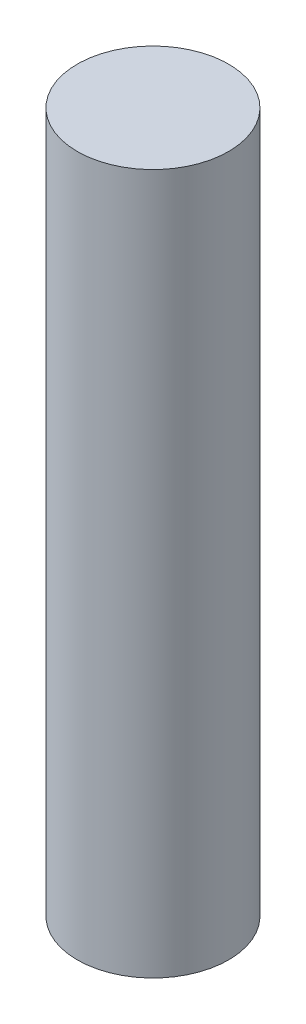
SolidWorks part; units mm, degrees
ref_plane "Front Plane" through (0, 0, 0) normal (0, 0, 1) x (1, 0, 0)
ref_plane "Top Plane" through (0, 0, 0) normal (0, 1, 0) x (1, 0, 0)
ref_plane "Right Plane" through (0, 0, 0) normal (1, 0, 0) x (0, 0, -1)
sketch "Sketch1" plane through (0, 0, 0) normal (0, 1, 0) x (1, 0, 0)
  circle A0 centre (0, 0) radius 0.4
  dimension "D1" = 0.8
extrude "Boss-Extrude1" add sketch "Sketch1" along normal blind 3.7
